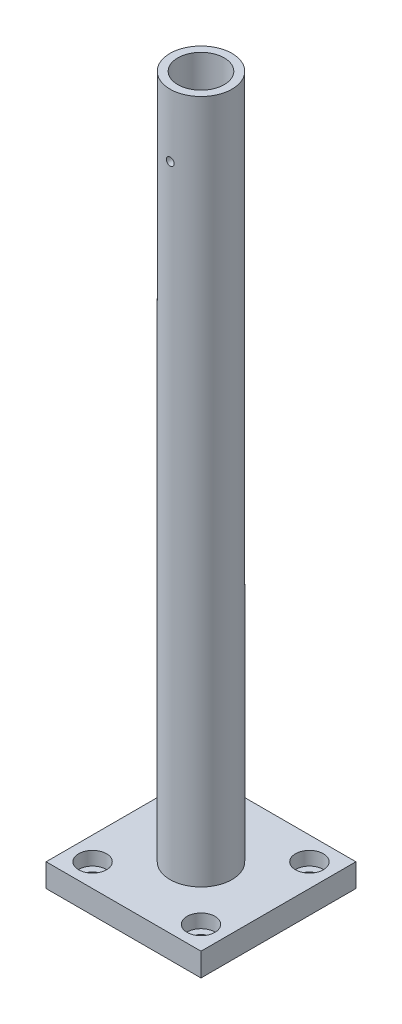
SolidWorks part; units mm, degrees
material "6061 Alloy"
ref_plane "Front Plane" through (0, 0, 0) normal (0, 0, 1) x (1, 0, 0)
ref_plane "Top Plane" through (0, 0, 0) normal (0, 1, 0) x (1, 0, 0)
ref_plane "Right Plane" through (0, 0, 0) normal (1, 0, 0) x (0, 0, -1)
sketch "Sketch4" plane through (0, 0, 0) normal (0, 1, 0) x (1, 0, 0)
  line L1 (0, 0) -> (100, 0)
  line L2 (0, 0) -> (0, 100)
  line L3 (0, 100) -> (100, 100)
  line L4 (100, 0) -> (100, 100)
  dimension "D1" = 100
  dimension "D2" = 100
extrude "Boss-Extrude4" add sketch "Sketch4" along normal blind 15
sketch "Sketch5" plane through (0, 15, 0) normal (0, 1, 0) x (1, 0, 0)
  line L2 (100, 0) -> (100, 100) construction
  circle A0 centre (50, 50) radius 20
  circle A1 centre (50, 50) radius 15
  point P7 (100, 50)
  dimension "D2" = 40
  dimension "D3" = 30
  dimension "D1" = 50
extrude "Boss-Extrude5" add sketch "Sketch5" along normal blind 442
sketch "Sketch8" plane through (0, 0, 0) normal (0, 0, 1) x (1, 0, 0)
  line L0 (0, 15) -> (100, 15) construction
  line L2 (100, 15) -> (100, 0) construction
  circle A0 centre (50, 416.5) radius 2.5
  dimension "D1" = 401.5
  dimension "D2" = 5
  dimension "D3" = 50
extrude "Cut-Extrude2" cut sketch "Sketch8" against normal blind 334
sketch "Sketch9" plane through (0, 15, 0) normal (0, 1, 0) x (1, 0, 0)
  line L0 (0, 100) -> (0, 0) construction
  line L1 (100, 100) -> (0, 100) construction
  line L2 (100, 0) -> (100, 100) construction
  line L3 (0, 0) -> (100, 0) construction
  circle A0 centre (15, 85) radius 4.5
  circle A1 centre (85, 85) radius 4.5
  circle A2 centre (85, 15) radius 4.5
  circle A3 centre (15, 15) radius 4.5
  dimension "D1" = 9
  dimension "D2" = 9
  dimension "D3" = 9
  dimension "D4" = 9
  dimension "D5" = 15
  dimension "D6" = 15
  dimension "D7" = 15
  dimension "D8" = 15
  dimension "D9" = 15
  dimension "D10" = 15
  dimension "D11" = 15
  dimension "D12" = 15
extrude "Cut-Extrude3" cut sketch "Sketch9" against normal blind 334
sketch "Sketch10" plane through (0, 15, 0) normal (0, 1, 0) x (1, 0, 0)
  circle A0 centre (15, 85) radius 9
  circle A1 centre (85, 85) radius 9
  circle A2 centre (85, 15) radius 9
  circle A3 centre (15, 15) radius 9
  dimension "D1" = 18
  dimension "D2" = 18
  dimension "D3" = 18
  dimension "D4" = 18
extrude "Cut-Extrude4" cut sketch "Sketch10" against normal blind 8.8
